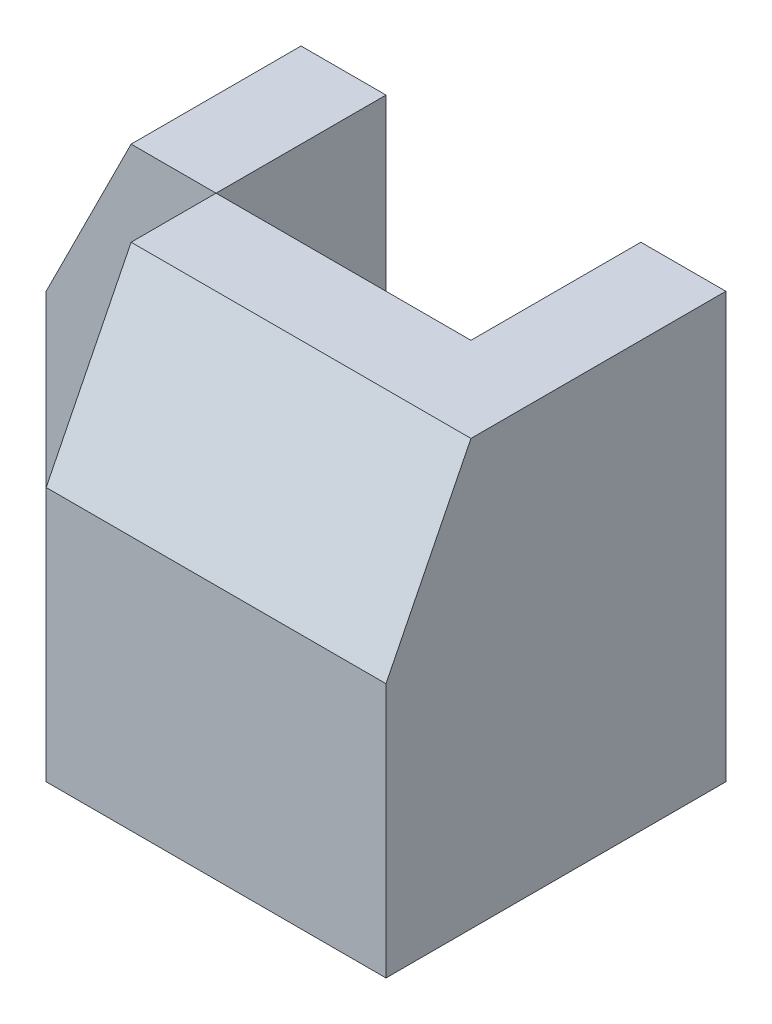
SolidWorks part; units mm, degrees
ref_plane "Front Plane" through (0, 0, 0) normal (0, 0, 1) x (1, 0, 0)
ref_plane "Top Plane" through (0, 0, 0) normal (0, 1, 0) x (1, 0, 0)
ref_plane "Right Plane" through (0, 0, 0) normal (1, 0, 0) x (0, 0, -1)
sketch "Sketch1" plane through (0, 0, 0) normal (0, 0, 1) x (1, 0, 0)
  line L1 (0, 0) -> (30, 0)
  line L2 (0, 0) -> (0, 25)
  line L3 (0, 25) -> (30, 25)
  line L4 (30, 0) -> (30, 25)
  dimension "D1" = 30
  dimension "D2" = 25
extrude "Boss-Extrude1" add sketch "Sketch1" along normal blind 20
sketch "Sketch2" plane through (0, 0, 20) normal (0, 0, 1) x (1, 0, 0)
  line L0 (30, 25) -> (0, 25) construction
  line L1 (0, 0) -> (10, 0)
  line L2 (0, 0) -> (0, 25)
  line L3 (0, 25) -> (10, 25)
  line L4 (10, 0) -> (10, 25)
  dimension "D1" = 10
extrude "Cut-Extrude1" cut sketch "Sketch2" against normal blind 10
sketch "Sketch3" plane through (0, 0, 10) normal (0, 0, 1) x (1, 0, 0)
  line L0 (0, 25) -> (5, 25)
  line L1 (10, 25) -> (0, 25) construction
  line L2 (5, 25) -> (0, 15)
  line L3 (0, 25) -> (0, 0) construction
  line L4 (0, 15) -> (0, 25)
  dimension "D1" = 10
  dimension "D2" = 5
extrude "Cut-Extrude2" cut sketch "Sketch3" against normal blind 10
sketch "Sketch4" plane through (0, 0, 0) normal (0, 0, -1) x (-1, 0, 0)
  line L0 (0, 0) -> (-30, 0) construction
  line L1 (-20, 0) -> (-10, 0)
  line L2 (-20, 0) -> (-20, 25)
  line L3 (-20, 25) -> (-10, 25)
  line L4 (-10, 0) -> (-10, 25)
  line L5 (-30, 25) -> (-5, 25) construction
  line L6 (0, 15) -> (0, 0) construction
  dimension "D1" = 10
  dimension "D2" = 10
extrude "Cut-Extrude4" cut sketch "Sketch4" against normal blind 10 contours L2 L1 L4 L3
sketch "Sketch5" plane through (0, 0, 0) normal (0, 0, -1) x (-1, 0, 0)
  line L0 (-25, 25) -> (-20, 15)
  line L1 (-30, 25) -> (-20, 25) construction
  line L2 (-20, 0) -> (-20, 25) construction
  line L3 (-20, 15) -> (-20, 25)
  line L4 (-20, 25) -> (-25, 25)
  dimension "D1" = 5
  dimension "D2" = 10
extrude "Cut-Extrude5" cut sketch "Sketch5" against normal blind 10
sketch "Sketch6" plane through (10, 0, 0) normal (-1, 0, 0) x (0, 0, 1)
  line L0 (15, 25) -> (20, 15)
  line L1 (10, 25) -> (20, 25) construction
  line L2 (20, 0) -> (20, 25) construction
  line L3 (20, 15) -> (20, 25)
  line L4 (20, 25) -> (15, 25)
  dimension "D1" = 10
  dimension "D2" = 5
extrude "Cut-Extrude6" cut sketch "Sketch6" against normal blind 20
